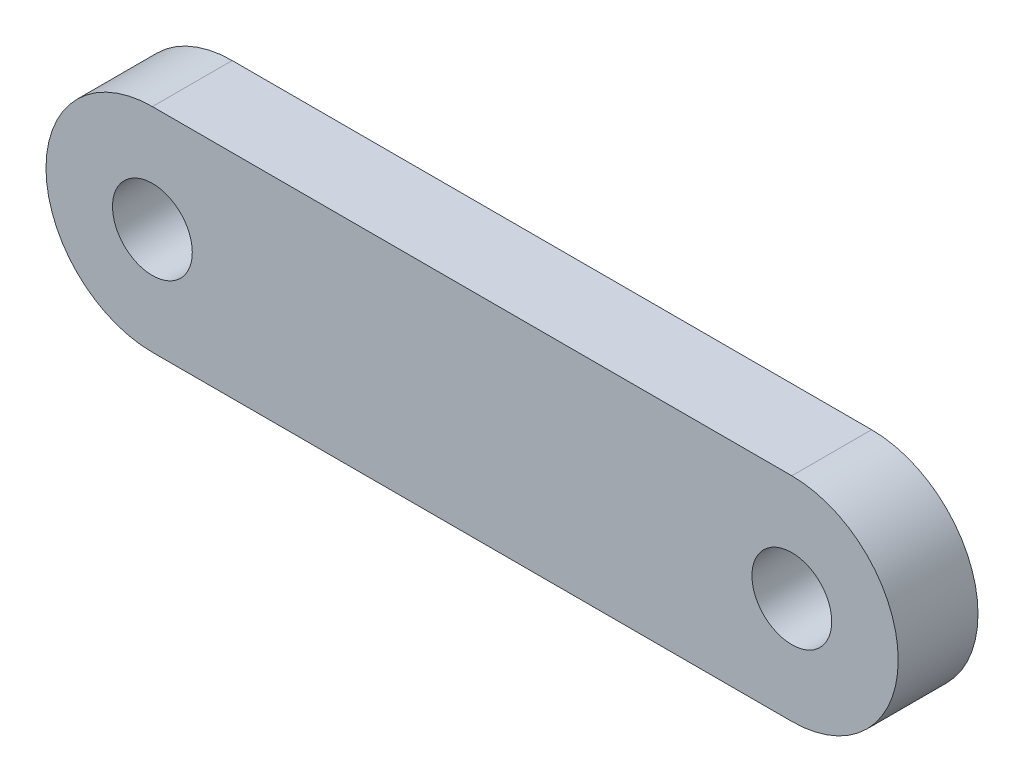
SolidWorks part; units mm, degrees
ref_plane "Front" through (0, 0, 0) normal (0, 0, 1) x (1, 0, 0)
ref_plane "Top" through (0, 0, 0) normal (0, 1, 0) x (1, 0, 0)
ref_plane "Right" through (0, 0, 0) normal (1, 0, 0) x (0, 0, -1)
sketch "Sketch1" plane through (0, 0, 0) normal (0, 0, 1) x (1, 0, 0)
  line L0 (0, 0) -> (12.02, 0) construction
  line L1 (0, 2) -> (12.02, 2)
  line L2 (0, -2) -> (12.02, -2)
  circle A0 centre (0, 0) radius 0.75
  circle A1 centre (12.02, 0) radius 0.75
  arc A2 (0, 2) -> (0, -2) centre (0, 0) ccw
  arc A3 (12.02, -2) -> (12.02, 2) centre (12.02, 0) ccw
  point P5 (6.01, 0)
  dimension "D1" = 1.5
  dimension "D3" = 2
  dimension "D2" = 12.02
extrude "Boss-Extrude1" add sketch "Sketch1" along normal mid plane 1.5
